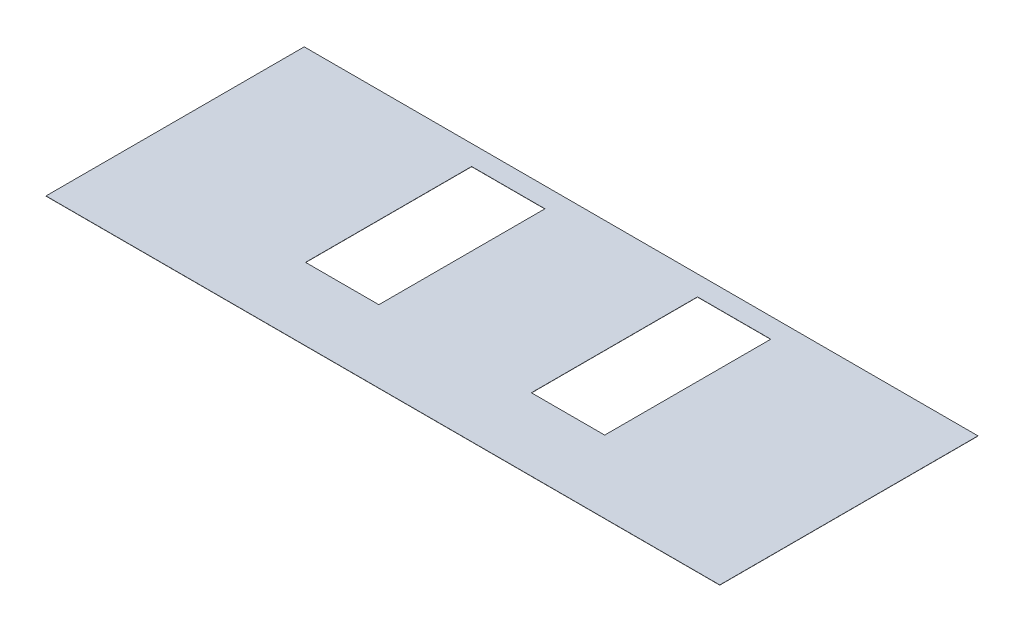
SolidWorks part; units mm, degrees
material "PE High Density Film"
ref_plane "Front Plane" through (0, 0, 0) normal (0, 0, 1) x (1, 0, 0)
ref_plane "Top Plane" through (0, 0, 0) normal (0, 1, 0) x (1, 0, 0)
ref_plane "Right Plane" through (0, 0, 0) normal (1, 0, 0) x (0, 0, -1)
sketch "Sketch1" plane through (0, 0, 0) normal (0, 1, 0) x (1, 0, 0)
  line L1 (-2743.2, -1051.306) -> (2743.2, -1051.306)
  line L2 (-2743.2, -1051.306) -> (-2743.2, 1051.306)
  line L3 (-2743.2, 1051.306) -> (2743.2, 1051.306)
  line L4 (2743.2, -1051.306) -> (2743.2, 1051.306)
  line L5 (-2743.2, -1051.306) -> (2743.2, 1051.306) construction
  line L6 (-2743.2, 1051.306) -> (2743.2, -1051.306) construction
  point P0 (0, 0)
  dimension "D1" = 2102.612
  dimension "D2" = 5486.4
extrude "Boss-Extrude1" add sketch "Sketch1" along normal blind 1.5875
sketch "Sketch2" plane through (0, 1.5875, 0) normal (0, 1, 0) x (1, 0, 0)
  line L1 (-621.03, 0) -> (621.03, 0) construction
  line L6 (-919.48, 1051.306) -> (-919.48, -252.9133) construction
  line L7 (919.48, 1051.306) -> (919.48, -252.9133) construction
  line L9 (-1217.93, 889.381) -> (-621.03, 889.381)
  line L10 (-1217.93, 889.381) -> (-1217.93, -463.169)
  line L11 (-1217.93, -463.169) -> (-621.03, -463.169)
  line L12 (-621.03, 889.381) -> (-621.03, -463.169)
  line L13 (-1217.93, 889.381) -> (-621.03, -463.169) construction
  line L14 (-1217.93, -463.169) -> (-621.03, 889.381) construction
  line L15 (621.03, 889.381) -> (1217.93, 889.381)
  line L16 (621.03, 889.381) -> (621.03, -463.169)
  line L17 (621.03, -463.169) -> (1217.93, -463.169)
  line L18 (1217.93, 889.381) -> (1217.93, -463.169)
  line L19 (621.03, 889.381) -> (1217.93, -463.169) construction
  line L20 (621.03, -463.169) -> (1217.93, 889.381) construction
  point P0 (422.8057, 0)
  point P3 (0, 0)
  point P14 (-919.48, 213.106)
  point P19 (919.48, 213.106)
  dimension "D1" = 1242.06
  dimension "D2" = 1352.55
  dimension "D3" = 596.9
  dimension "D4" = 463.169
extrude "Cut-Extrude1" cut sketch "Sketch2" against normal through all both and the other way through all
